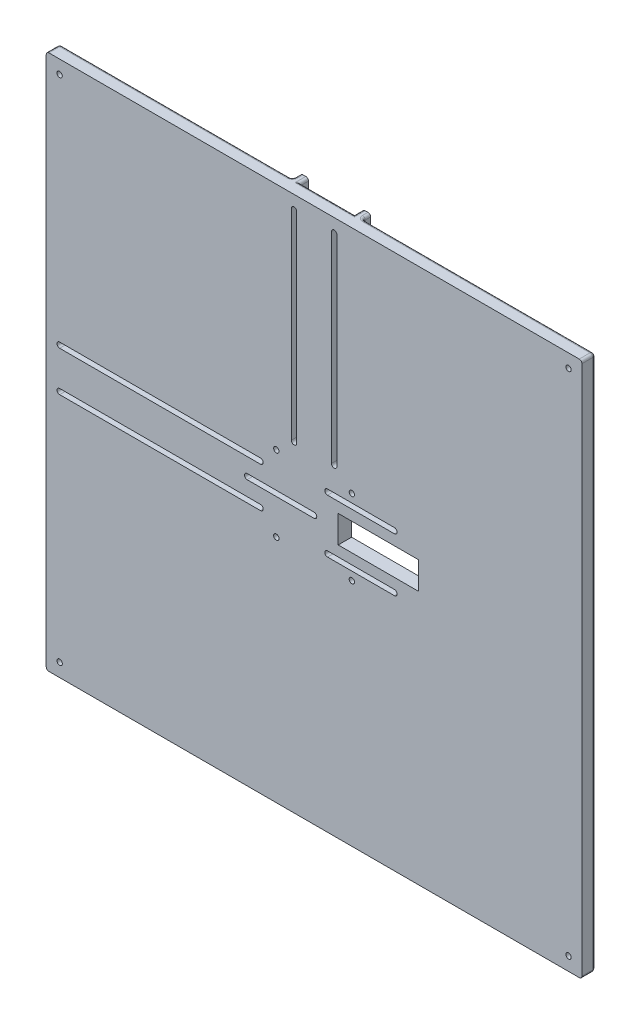
SolidWorks part; units mm, degrees
ref_plane "Plan de face" through (0, 0, 0) normal (0, 0, 1) x (1, 0, 0)
ref_plane "Plan de dessus" through (0, 0, 0) normal (0, 1, 0) x (1, 0, 0)
ref_plane "Plan de droite" through (0, 0, 0) normal (1, 0, 0) x (0, 0, -1)
sketch "Esquisse1" plane through (0, 0, 0) normal (0, 0, 1) x (1, 0, 0)
  line L1 (-100, 100) -> (100, 100)
  line L2 (-100, 100) -> (-100, -100)
  line L3 (-100, -100) -> (100, -100)
  line L4 (100, 100) -> (100, -100)
  dimension "D1" = 200
  dimension "D2" = 200
  dimension "D3" = 100
  dimension "D4" = 100
extrude "Boss.-Extru.1" add sketch "Esquisse1" along normal blind 5
sketch "Esquisse2" plane through (0, 0, 0) normal (0, 0, -1) x (-1, 0, 0)
  line L1 (20, 10.1) -> (100, 10.1)
  line L4 (100, 10.1) -> (100, 13.1)
  line L5 (100, -13.1) -> (20, -13.1)
  line L6 (100, -13.1) -> (100, -10.1)
  line L7 (100, -10.1) -> (20, -10.1)
  line L19 (100, 100) -> (100, -100) construction
  line L20 (100, -100) -> (-100, -100) construction
  line L24 (13.1, 20) -> (13.1, 100)
  line L25 (-100, 100) -> (100, 100) construction
  line L26 (10.1, 20) -> (10.1, 100)
  line L28 (-13.1, 100) -> (-10.1, 100)
  line L29 (10.1, 100) -> (13.1, 100)
  line L31 (-10.1, 100) -> (-10.1, 20)
  line L32 (-13.1, 100) -> (-13.1, 20)
  line L33 (-10.1, 20) -> (-13.1, 20)
  line L34 (-100, -100) -> (-100, 100) construction
  line L35 (20, -10.1) -> (20, -13.1)
  line L36 (100, 13.1) -> (20, 13.1)
  line L37 (20, 13.1) -> (20, 10.1)
  line L38 (13.1, 20) -> (10.1, 20)
  dimension "D1" = 20.2
  dimension "D2" = 3
  dimension "D3" = 3
  dimension "D4" = 89.9
  dimension "D5" = 3
  dimension "D6" = 3
  dimension "D7" = 20.2
  dimension "D8" = 86.9
  dimension "D9" = 80
  dimension "D10" = 80
extrude "Boss.-Extru.2" add sketch "Esquisse2" along normal blind 3
fillet "Congé1" radius 1 32 edges at (-13.1, 60, 0) (-60, -13.1, 0) (-13.1, 100, -1.5) (-100, -13.1, -1.5) (100, -100, 2.5) (100, 100, 2.5) (100, 0, 0) (0, 100, 0) (-100, 0, 0) (-56.55, 100, 0) (-100, 56.55, 0) (-100, 100, 2.5) (56.55, 100, 0) (0, -100, 0) (-100, -56.55, 0) (-100, -100, 2.5) (-10.1, 100, -1.5) (-100, 10.1, -1.5) (-100, -10.1, -1.5) (13.1, 100, -1.5) (10.1, 100, -1.5) (13.1, 60, 0) (-100, 13.1, -1.5) (-60, 13.1, 0) (-20, -11.6, 0) (11.6, 20, 0) (-11.6, 20, 0) (-20, 11.6, 0) (-20, -13.1, -1.5) (13.1, 20, -1.5) (-13.1, 20, -1.5) (-20, 13.1, -1.5)
sketch "Esquisse4" plane through (0, 0, 0) normal (0, 0, -1) x (-1, 0, 0)
  line L4 (-100, -99) -> (-100, 99) construction
  line L5 (99, -100) -> (-99, -100) construction
  line L6 (-99, 100) -> (-14.1, 100) construction
  line L7 (100, -14.1) -> (100, -99) construction
  circle A0 centre (-14.1, 14.1) radius 1
  circle A1 centre (14.1, 14.1) radius 1
  circle A2 centre (14.1, -14.1) radius 1
  circle A3 centre (-14.1, -14.1) radius 1
  circle A4 centre (-95, -95) radius 1
  circle A5 centre (-95, 95) radius 1
  circle A6 centre (95, -95) radius 1
  circle A7 centre (95, 95) radius 1
  dimension "D1" = 2
  dimension "D4" = 4
  dimension "D5" = 4
  dimension "D6" = 5
  dimension "D7" = 5
  dimension "D8" = 5
  dimension "D9" = 5
  dimension "D10" = 4
  dimension "D11" = 4
extrude "Enlèv. mat.-Extru.1" cut sketch "Esquisse4" against normal up to next
sketch "Esquisse5" plane through (0, 0, 0) normal (0, 0, -1) x (-1, 0, 0)
  line L0 (-7.5, 95) -> (-7.5, 20) construction
  line L1 (-6.5, 95) -> (-6.5, 20)
  line L2 (-8.5, 95) -> (-8.5, 20)
  line L3 (7.5, 95) -> (7.5, 20) construction
  line L4 (8.5, 95) -> (8.5, 20)
  line L5 (6.5, 95) -> (6.5, 20)
  line L9 (10.1, 99) -> (10.1, 19) construction
  line L10 (-10.1, 100) -> (10.1, 100) construction
  line L11 (-10.1, 19) -> (-10.1, 99) construction
  line L12 (-99, 100) -> (-14.1, 100) construction
  arc A0 (-6.5, 95) -> (-8.5, 95) centre (-7.5, 95) ccw
  arc A1 (-8.5, 20) -> (-6.5, 20) centre (-7.5, 20) ccw
  arc A2 (8.5, 95) -> (6.5, 95) centre (7.5, 95) ccw
  arc A3 (6.5, 20) -> (8.5, 20) centre (7.5, 20) ccw
  point P2 (-7.5, 57.5)
  point P7 (7.5, 57.5)
  dimension "D1" = 1
  dimension "D2" = 1
  dimension "D3" = 2.6
  dimension "D4" = 5
  dimension "D6" = 2.6
  dimension "D7" = 80
extrude "Enlèv. mat.-Extru.2" cut sketch "Esquisse5" against normal through all
sketch "Esquisse6" plane through (0, 0, 0) normal (0, 0, -1) x (-1, 0, 0)
  line L0 (95, -7.5) -> (20, -7.5) construction
  line L1 (95, -8.5) -> (20, -8.5)
  line L2 (95, -6.5) -> (20, -6.5)
  line L3 (20, 7.5) -> (95, 7.5) construction
  line L4 (20, 8.5) -> (95, 8.5)
  line L5 (20, 6.5) -> (95, 6.5)
  line L6 (99, -10.1) -> (19, -10.1) construction
  line L7 (19, 10.1) -> (99, 10.1) construction
  line L8 (100, 10.1) -> (100, -10.1) construction
  arc A0 (95, -8.5) -> (95, -6.5) centre (95, -7.5) ccw
  arc A1 (20, -6.5) -> (20, -8.5) centre (20, -7.5) ccw
  arc A2 (20, 8.5) -> (20, 6.5) centre (20, 7.5) ccw
  arc A3 (95, 6.5) -> (95, 8.5) centre (95, 7.5) ccw
  point P2 (57.5, -7.5)
  point P7 (57.5, 7.5)
  dimension "D1" = 1
  dimension "D2" = 1
  dimension "D3" = 2.6
  dimension "D4" = 2.6
  dimension "D5" = 5
  dimension "D7" = 80
extrude "Enlèv. mat.-Extru.3" cut sketch "Esquisse6" against normal up to next
sketch "Esquisse9" plane through (0, 0, 5) normal (0, 0, 1) x (1, 0, 0)
  line L0 (-25, 0) -> (0, 0) construction
  line L1 (-25, 1) -> (0, 1)
  line L2 (-25, -1) -> (0, -1)
  line L3 (5, 10) -> (30, 10) construction
  line L4 (5, 11) -> (30, 11)
  line L5 (5, 9) -> (30, 9)
  line L6 (5, -10) -> (30, -10) construction
  line L7 (5, -9) -> (30, -9)
  line L8 (5, -11) -> (30, -11)
  arc A0 (-25, 1) -> (-25, -1) centre (-25, 0) ccw
  arc A1 (0, -1) -> (0, 1) centre (0, 0) ccw
  arc A2 (5, 11) -> (5, 9) centre (5, 10) ccw
  arc A3 (30, 9) -> (30, 11) centre (30, 10) ccw
  arc A4 (5, -9) -> (5, -11) centre (5, -10) ccw
  arc A5 (30, -11) -> (30, -9) centre (30, -10) ccw
  point P3 (-12.5, 0)
  point P8 (17.5, 10)
  point P15 (17.5, -10)
  point P22 (0, 0)
  dimension "D4" = 25
  dimension "D5" = 30
  dimension "D1" = 2
  dimension "D2" = 2
  dimension "D3" = 2
  dimension "D6" = 25
  dimension "D7" = 10
  dimension "D8" = 10
  dimension "D9" = 25
extrude "Enlèv. mat.-Extru.5" cut sketch "Esquisse9" against normal up to next
sketch "Esquisse11" plane through (0, 0, 0) normal (0, 0, -1) x (-1, 0, 0)
  line L1 (-9, 5.1) -> (-39, 5.1)
  line L2 (-9, 5.1) -> (-9, -5.1)
  line L3 (-9, -5.1) -> (-39, -5.1)
  line L4 (-39, 5.1) -> (-39, -5.1)
  dimension "D1" = 9
  dimension "D2" = 10.2
  dimension "D3" = 5.1
  dimension "D4" = 30
extrude "Enlèv. mat.-Extru.7" cut sketch "Esquisse11" against normal up to next
sketch "Esquisse12" plane through (0, 0, 0) normal (0, 0, -1) x (-1, 0, 0)
  line L1 (-33, 12.1) -> (-2, 12.1)
  line L2 (-33, 12.1) -> (-33, 7.9)
  line L3 (-33, 7.9) -> (-2, 7.9)
  line L4 (-2, 12.1) -> (-2, 7.9)
  line L5 (-33, -7.9) -> (-2, -7.9)
  line L6 (-33, -7.9) -> (-33, -12.1)
  line L7 (-33, -12.1) -> (-2, -12.1)
  line L8 (-2, -7.9) -> (-2, -12.1)
  line L9 (-3, 2.1) -> (28, 2.1)
  line L10 (-3, 2.1) -> (-3, -2.1)
  line L11 (-3, -2.1) -> (28, -2.1)
  line L12 (28, 2.1) -> (28, -2.1)
  arc A0 (-30, 11) -> (-30, 9) centre (-30, 10) ccw construction
  arc A1 (-30, -9) -> (-30, -11) centre (-30, -10) ccw construction
  arc A2 (-5, -11) -> (-5, -9) centre (-5, -10) ccw construction
  arc A3 (0, 1) -> (0, -1) centre (0, 0) ccw construction
  arc A4 (25, -1) -> (25, 1) centre (25, 0) ccw construction
  arc A5 (-5, 9) -> (-5, 11) centre (-5, 10) ccw construction
  point P15 (-31, 10)
  point P20 (-31, -10)
  dimension "D7" = 3
  dimension "D8" = 3
  dimension "D9" = 3
  dimension "D10" = 3
  dimension "D11" = 3
  dimension "D12" = 3
  dimension "D1" = 2.1
  dimension "D2" = 4.2
  dimension "D3" = 2.1
  dimension "D4" = 4.2
  dimension "D5" = 2.1
  dimension "D6" = 4.2
extrude "Enlèv. mat.-Extru.9" cut sketch "Esquisse12" against normal blind 2
fillet "Congé2" radius 0.5 11 edges at (33, -12.1, 1) (33, -7.9, 1) (2, -7.9, 1) (2, -12.1, 1) (-28, -2.1, 1) (-28, 2.1, 1) (3, -2.1, 1) (3, 2.1, 1) (2, 12.1, 1) (33, 7.9, 1) (33, 12.1, 1)
